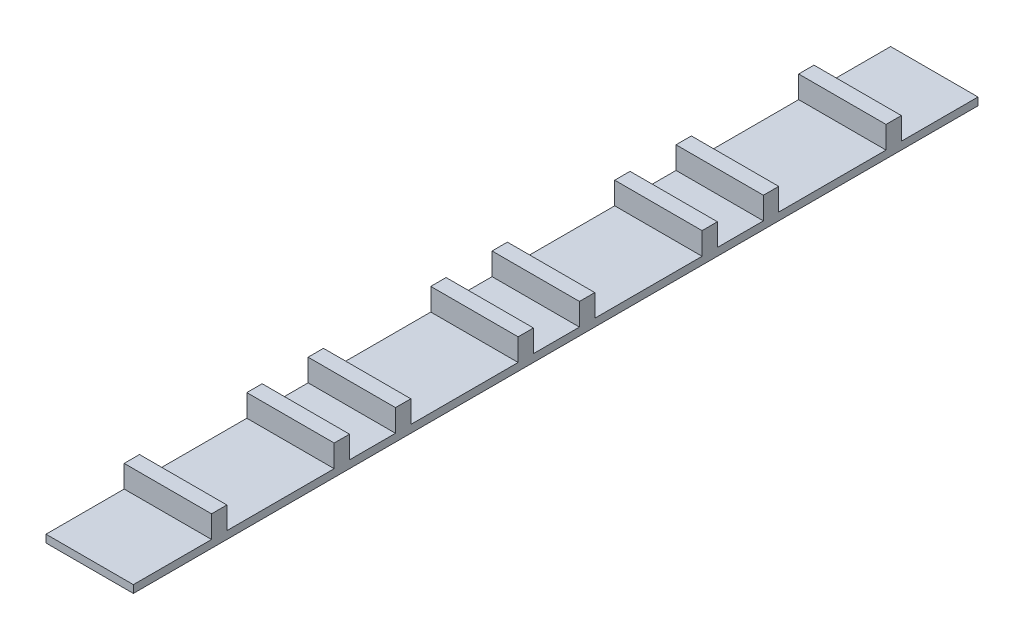
SolidWorks part; units mm, degrees
ref_plane "Front Plane" through (0, 0, 0) normal (0, 0, 1) x (1, 0, 0)
ref_plane "Top Plane" through (0, 0, 0) normal (0, 1, 0) x (1, 0, 0)
ref_plane "Right Plane" through (0, 0, 0) normal (1, 0, 0) x (0, 0, -1)
sketch "Sketch1" plane through (0, 0, 0) normal (0, 0, 1) x (1, 0, 0)
  line L1 (0, 0) -> (14.478, 0)
  line L2 (0, 0) -> (0, 1.27)
  line L3 (0, 1.27) -> (14.478, 1.27)
  line L4 (14.478, 0) -> (14.478, 1.27)
  dimension "D1" = 1.27
  dimension "D2" = 14.478
extrude "Boss-Extrude1" add sketch "Sketch1" along normal blind 139.954
sketch "Sketch2" plane through (0, 1.27, 0) normal (0, 1, 0) x (1, 0, 0)
  line L0 (0, -139.954) -> (0, 0) construction
  line L1 (0, -12.7) -> (14.478, -12.7)
  line L2 (0, -12.7) -> (0, -15.24)
  line L3 (0, -15.24) -> (14.478, -15.24)
  line L4 (14.478, -12.7) -> (14.478, -15.24)
  line L5 (14.478, -139.954) -> (14.478, 0) construction
  line L6 (14.478, 0) -> (0, 0) construction
  line L7 (0, -33.02) -> (14.478, -33.02)
  line L8 (0, -33.02) -> (0, -35.56)
  line L9 (0, -35.56) -> (14.478, -35.56)
  line L10 (14.478, -33.02) -> (14.478, -35.56)
  dimension "D1" = 2.54
  dimension "D2" = 12.7
  dimension "D3" = 17.78
extrude "Boss-Extrude2" add sketch "Sketch2" along normal blind 3.683
pattern_linear "LPattern1" count 4 spacing 30.48 along (0, 0, 1) of "Boss-Extrude2"
